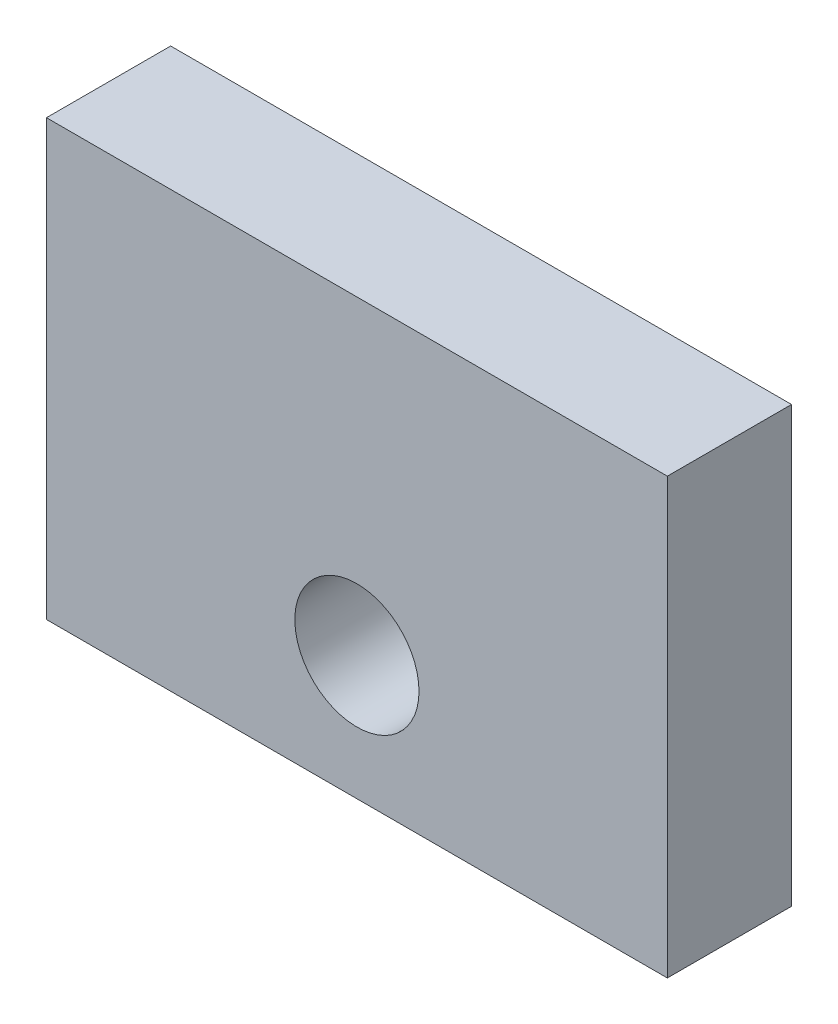
SolidWorks part; units mm, degrees
ref_plane "Front Plane" through (0, 0, 0) normal (0, 0, 1) x (1, 0, 0)
ref_plane "Top Plane" through (0, 0, 0) normal (0, 1, 0) x (1, 0, 0)
ref_plane "Right Plane" through (0, 0, 0) normal (1, 0, 0) x (0, 0, -1)
sketch "Sketch1" plane through (0, 0, 0) normal (0, 0, 1) x (1, 0, 0)
  line L0 (5, 3) -> (5, 7) construction
  line L1 (0, 0) -> (10, 0)
  line L2 (0, 0) -> (0, 7)
  line L3 (0, 7) -> (10, 7)
  line L4 (10, 0) -> (10, 7)
  circle A0 centre (5, 2) radius 1
  dimension "D3" = 2
  dimension "D4" = 2
  dimension "D1" = 10
  dimension "D2" = 7
extrude "Boss-Extrude1" add sketch "Sketch1" along normal blind 2
